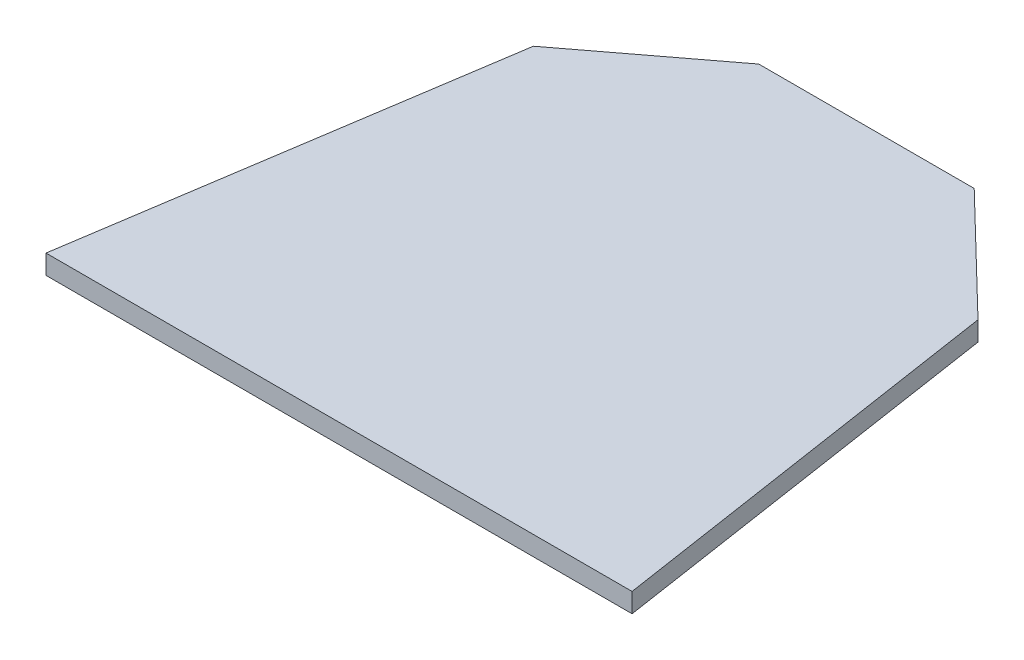
SolidWorks part; units mm, degrees
ref_plane "Plan de face" through (0, 0, 0) normal (0, 0, 1) x (1, 0, 0)
ref_plane "Plan de dessus" through (0, 0, 0) normal (0, 1, 0) x (1, 0, 0)
ref_plane "Plan de droite" through (0, 0, 0) normal (1, 0, 0) x (0, 0, -1)
sketch "Esquisse1" plane through (0, 0, 0) normal (0, 1, 0) x (1, 0, 0)
  line L0 (60.5101, 0) -> (54.0746, 42.1493)
  line L1 (54.0746, 42.1493) -> (42.1383, 53.6939)
  line L2 (42.1383, 53.6939) -> (19.8982, 53.6939)
  line L3 (19.8982, 53.6939) -> (6.6655, 43.6554)
  line L4 (6.6655, 43.6554) -> (0, 0)
  line L5 (0, 0) -> (60.5101, 0)
  point P6 (0, 0)
extrude "Boss.-Extru.1" add sketch "Esquisse1" along normal blind 2
